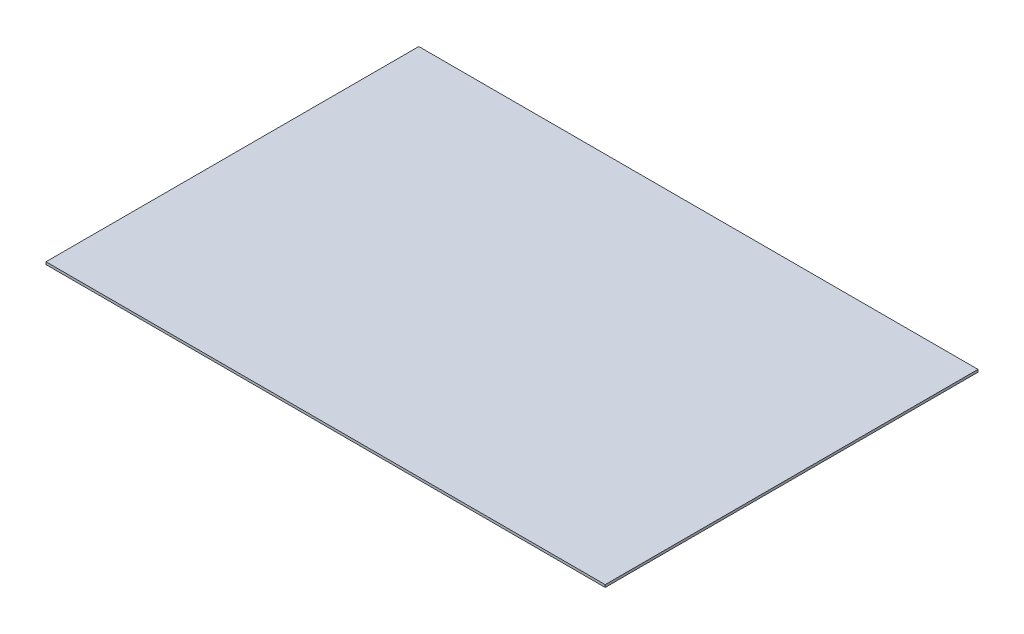
SolidWorks part; units mm, degrees
ref_plane "Front Plane" through (0, 0, 0) normal (0, 0, 1) x (1, 0, 0)
ref_plane "Top Plane" through (0, 0, 0) normal (0, 1, 0) x (1, 0, 0)
ref_plane "Right Plane" through (0, 0, 0) normal (1, 0, 0) x (0, 0, -1)
sketch "Sketch1" plane through (0, 0, 0) normal (0, 1, 0) x (1, 0, 0)
  line L1 (114.3, 76.2) -> (-114.3, 76.2)
  line L2 (114.3, 76.2) -> (114.3, -76.2)
  line L3 (114.3, -76.2) -> (-114.3, -76.2)
  line L4 (-114.3, 76.2) -> (-114.3, -76.2)
  line L5 (114.3, 76.2) -> (-114.3, -76.2) construction
  line L6 (114.3, -76.2) -> (-114.3, 76.2) construction
  point P0 (0, 0)
  dimension "D1" = 228.6
  dimension "D2" = 152.4
extrude "Boss-Extrude1" add sketch "Sketch1" along normal blind 1.016
